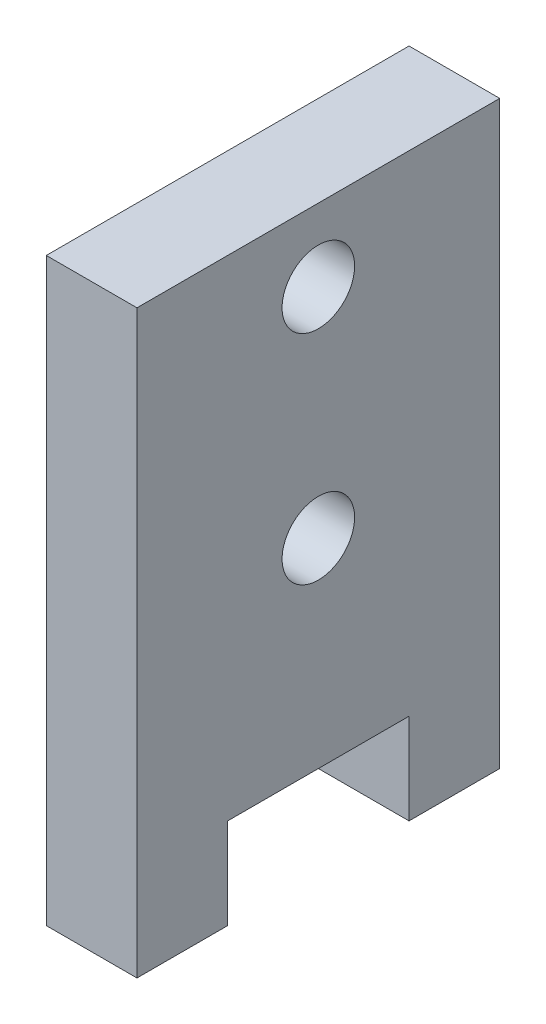
SolidWorks part; units mm, degrees
ref_plane "Front Plane" through (0, 0, 0) normal (0, 0, 1) x (1, 0, 0)
ref_plane "Top Plane" through (0, 0, 0) normal (0, 1, 0) x (1, 0, 0)
ref_plane "Right Plane" through (0, 0, 0) normal (1, 0, 0) x (0, 0, -1)
sketch "Sketch1" plane through (0, 0, 0) normal (1, 0, 0) x (0, 0, -1)
  line L1 (-6.35, -10.16) -> (6.35, -10.16)
  line L2 (-6.35, -10.16) -> (-6.35, 10.16)
  line L3 (-6.35, 10.16) -> (6.35, 10.16)
  line L4 (6.35, -10.16) -> (6.35, 10.16)
  line L5 (-6.35, -10.16) -> (6.35, 10.16) construction
  line L6 (-6.35, 10.16) -> (6.35, -10.16) construction
  point P0 (0, 0)
  dimension "D1" = 20.32
  dimension "D2" = 12.7
extrude "Boss-Extrude1" add sketch "Sketch1" along normal blind 3.175
sketch "Sketch2" plane through (3.175, 0, 0) normal (1, 0, 0) x (0, 0, -1)
  line L0 (-6.35, -10.16) -> (6.35, -10.16) construction
  line L1 (-3.175, -10.16) -> (3.175, -10.16)
  line L2 (-3.175, -10.16) -> (-3.175, -6.985)
  line L3 (-3.175, -6.985) -> (3.175, -6.985)
  line L4 (3.175, -10.16) -> (3.175, -6.985)
  line L5 (-6.35, 10.16) -> (-6.35, -10.16) construction
  line L6 (6.35, -10.16) -> (6.35, 10.16) construction
  dimension "D1" = 3.175
  dimension "D2" = 3.175
  dimension "D3" = 3.175
extrude "Cut-Extrude1" cut sketch "Sketch2" against normal through all
sketch "Sketch3" plane through (3.175, 0, 0) normal (1, 0, 0) x (0, 0, -1)
  line L0 (0, 29.8355) -> (0, -29.8355) construction
  circle A0 centre (0, 0) radius 1.27
  circle A2 centre (0, 7.62) radius 1.27
  point P4 (0, 0)
  dimension "D1" = 2
  dimension "D2" = 2.54
extrude "Cut-Extrude2" cut sketch "Sketch3" against normal through all
